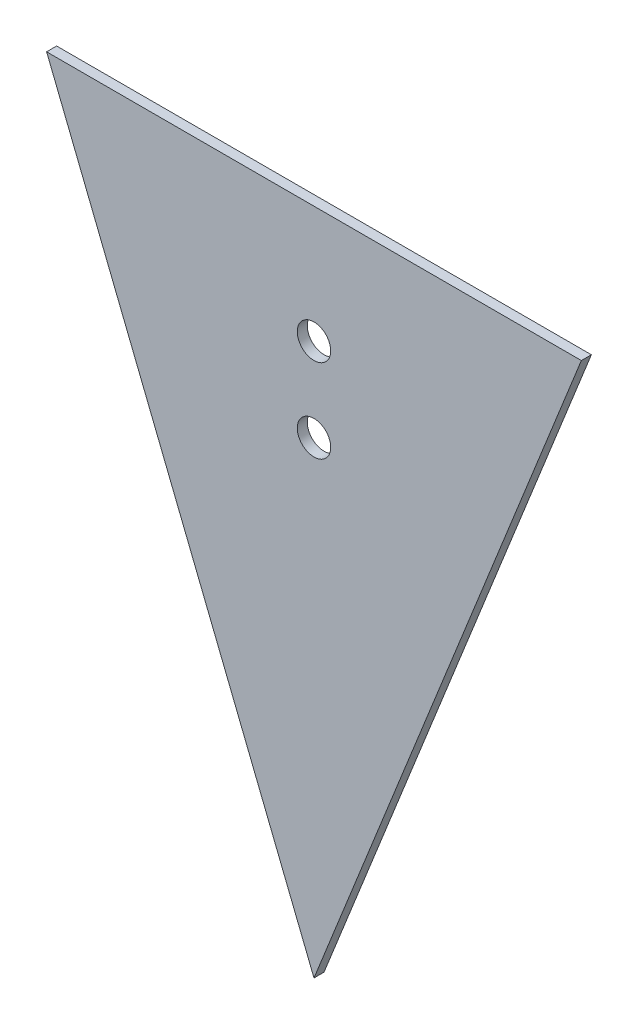
SolidWorks part; units mm, degrees
ref_plane "Front Plane" through (0, 0, 0) normal (0, 0, 1) x (1, 0, 0)
ref_plane "Top Plane" through (0, 0, 0) normal (0, 1, 0) x (1, 0, 0)
ref_plane "Right Plane" through (0, 0, 0) normal (1, 0, 0) x (0, 0, -1)
sketch "Sketch1" plane through (0, 0, 0) normal (0, 0, 1) x (1, 0, 0)
  line L0 (-26.9014, -70.2817) -> (53.0986, 129.7183)
  line L1 (53.0986, 129.7183) -> (-106.9014, 129.7183)
  line L2 (-106.9014, 129.7183) -> (-26.9014, -70.2817)
  dimension "D1" = 160
  dimension "D2" = 200
  dimension "D3" = 80
extrude "Boss-Extrude1" add sketch "Sketch1" along normal blind 3
sketch "Sketch2" plane through (0, 0, 3) normal (0, 0, 1) x (1, 0, 0)
  line L0 (53.0986, 129.7183) -> (-106.9014, 129.7183) construction
  circle A0 centre (-26.9014, 94.7183) radius 5
  circle A1 centre (-26.9014, 69.7183) radius 5
  dimension "D1" = 10
  dimension "D2" = 35
  dimension "D3" = 80
  dimension "D4" = 80
extrude "Cut-Extrude1" cut sketch "Sketch2" against normal up to next
